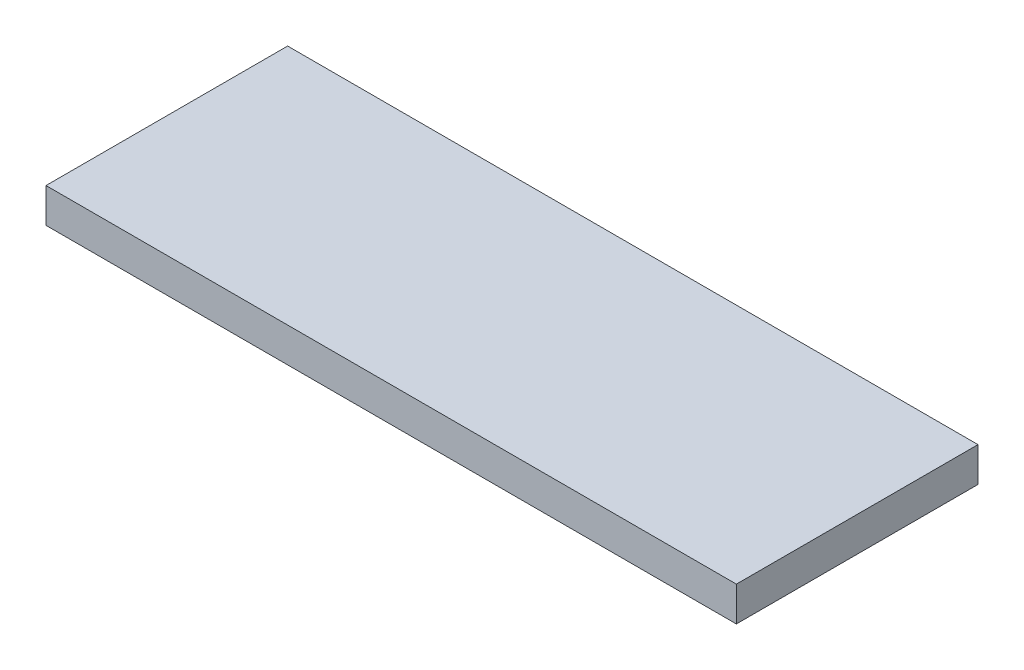
SolidWorks part; units mm, degrees
ref_plane "Front Plane" through (0, 0, 0) normal (0, 0, 1) x (1, 0, 0)
ref_plane "Top Plane" through (0, 0, 0) normal (0, 1, 0) x (1, 0, 0)
ref_plane "Right Plane" through (0, 0, 0) normal (1, 0, 0) x (0, 0, -1)
sketch "Sketch1" plane through (0, 0, 0) normal (0, 1, 0) x (1, 0, 0)
  line L0 (63.5, 0) -> (-63.5, 0) construction
  line L1 (-63.5, -22.225) -> (63.5, -22.225)
  line L2 (-63.5, -22.225) -> (-63.5, 22.225)
  line L3 (-63.5, 22.225) -> (63.5, 22.225)
  line L4 (63.5, -22.225) -> (63.5, 22.225)
  line L5 (-63.5, -22.225) -> (63.5, 22.225) construction
  line L6 (-63.5, 22.225) -> (63.5, -22.225) construction
  line L7 (60.325, -22.225) -> (60.325, 22.225) construction
  line L8 (-60.325, -22.225) -> (-60.325, 22.225) construction
  point P0 (0, 0)
  dimension "D1" = 44.45
  dimension "D2" = 127
  dimension "D3" = 3.175
  dimension "D4" = 3.175
extrude "Boss-Extrude1" add sketch "Sketch1" along normal blind 6.35
sketch "Sketch2" plane through (0, 6.35, 0) normal (0, 1, 0) x (1, 0, 0)
  line L0 (0, -22.225) -> (0, 22.225) construction
  line L1 (-63.5, -22.225) -> (63.5, -22.225) construction
  line L2 (63.5, 22.225) -> (-63.5, 22.225) construction
  circle A0 centre (0, 12.7) radius 1.7272
  dimension "D1" = 9.525
